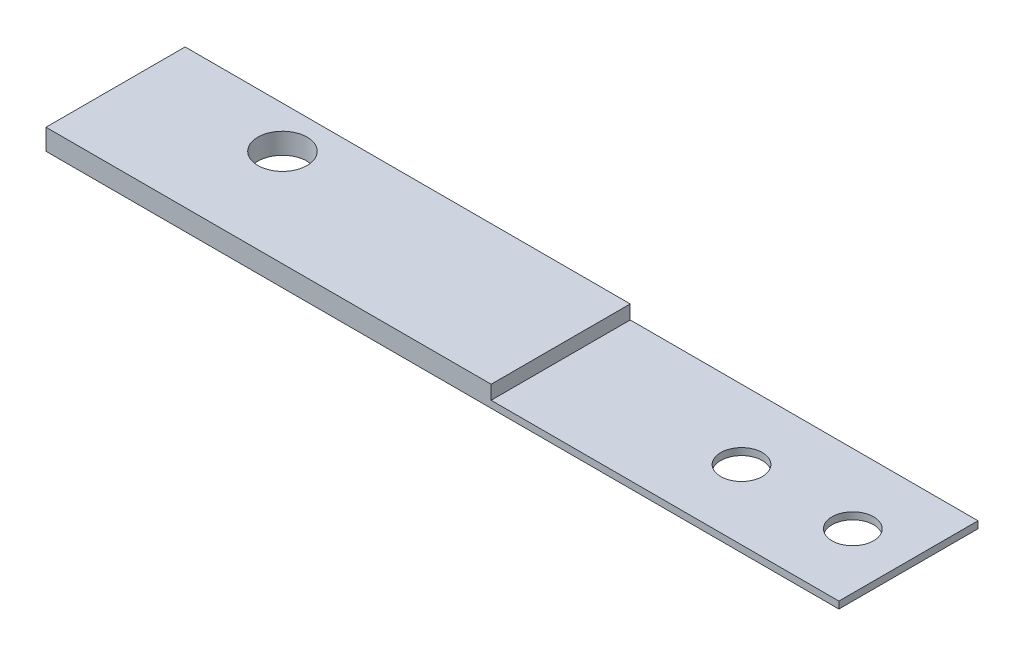
SolidWorks part; units mm, degrees
ref_plane "Front Plane" through (0, 0, 0) normal (0, 0, 1) x (1, 0, 0)
ref_plane "Top Plane" through (0, 0, 0) normal (0, 1, 0) x (1, 0, 0)
ref_plane "Right Plane" through (0, 0, 0) normal (1, 0, 0) x (0, 0, -1)
sketch "Sketch1" plane through (0, 0, 0) normal (0, 1, 0) x (1, 0, 0)
  line L1 (0, 0) -> (72.39, 0)
  line L2 (0, 0) -> (0, -12.7)
  line L3 (0, -12.7) -> (72.39, -12.7)
  line L4 (72.39, 0) -> (72.39, -12.7)
  dimension "D1" = 72.39
  dimension "D2" = 12.7
extrude "Boss-Extrude1" add sketch "Sketch1" along normal blind 0.635 contours L1 L4 L3 L2
sketch "Sketch2" plane through (0, 0.635, 0) normal (0, 1, 0) x (1, 0, 0)
  line L0 (0, -12.7) -> (72.39, -12.7) construction
  line L1 (0, 0) -> (40.64, 0)
  line L2 (0, 0) -> (0, -12.7)
  line L3 (0, -12.7) -> (40.64, -12.7)
  line L4 (40.64, 0) -> (40.64, -12.7)
  line L5 (72.39, 0) -> (72.39, -12.7) construction
  dimension "D1" = 31.75
extrude "Boss-Extrude2" add sketch "Sketch2" along normal blind 1.27
sketch "Sketch3" plane through (0, 0, 0) normal (0, -1, 0) x (1, 0, 0)
  line L0 (72.39, 0) -> (72.39, 12.7) construction
  line L1 (0, 0) -> (0, 12.7) construction
  line L2 (0, 0) -> (72.39, 0) construction
  line L3 (0, 12.7) -> (72.39, 12.7) construction
  point P0 (67.31, 6.35)
  point P1 (57.15, 6.35)
  point P2 (12.7, 3.81)
  dimension "D1" = 5.08
  dimension "D2" = 10.16
  dimension "D3" = 12.7
  dimension "D4" = 3.81
  dimension "D5" = 6.35
  dimension "D6" = 6.35
hole_wizard "#6 Clearance Hole1" positions "Sketch4" profile "Sketch5" hole size "#6" standard "ANSI Inch" end condition through all
sketch "Sketch4" plane through (0, 0, 0) normal (0, -1, 0) x (-1, 0, 0)
  point P0 (-67.31, -6.35)
  point P3 (-57.15, -6.35)
sketch "Sketch5" plane through (67.31, 0, 6.35) normal (1, 0, 0) x (0, 0, -1)
  line L0 (0, 0) -> (0, 1.905)
  line L1 (0, 1.905) -> (1.8986, 1.905)
  line L2 (1.8986, 1.905) -> (1.8986, 0)
  line L5 (1.8986, 0) -> (0, 0)
  line L11 (0, -6.35) -> (0, 107.95) construction
  dimension "Thru Hole Dia." = 3.7973
  dimension "Thru Hole Depth" = 1.905
hole_wizard "#8 Clearance Hole1" positions "Sketch6" profile "Sketch7" hole size "#8" standard "ANSI Inch" end condition through all
sketch "Sketch6" plane through (0, 0, 0) normal (0, -1, 0) x (-1, 0, 0)
  point P0 (-12.7, -3.81)
sketch "Sketch7" plane through (12.7, 0, 3.81) normal (1, 0, 0) x (0, 0, -1)
  line L0 (0, 0) -> (0, 1.905)
  line L1 (0, 1.905) -> (2.2479, 1.905)
  line L2 (2.2479, 1.905) -> (2.2479, 0)
  line L5 (2.2479, 0) -> (0, 0)
  line L11 (0, -6.35) -> (0, 107.95) construction
  dimension "Thru Hole Dia." = 4.4958
  dimension "Thru Hole Depth" = 1.905
sketch "Sketch9" plane through (0, 0, 0) normal (-1, 0, 0) x (0, 0, 1)
  line L0 (0, 0) -> (0.2933, 0.508)
  line L1 (0.2933, 0.508) -> (0.5866, 0)
  line L2 (0, 0) -> (12.7, 0) construction
  line L3 (0.5866, 0) -> (0.8799, 0.508)
  line L4 (0.8799, 0.508) -> (1.1732, 0)
  line L5 (1.27, 0) -> (1.5633, 0.508)
  line L6 (1.5633, 0.508) -> (1.8566, 0)
  line L7 (1.8566, 0) -> (2.1499, 0.508)
  line L8 (2.1499, 0.508) -> (2.4432, 0)
  line L9 (2.54, 0) -> (2.8333, 0.508)
  line L10 (2.8333, 0.508) -> (3.1266, 0)
  line L11 (3.1266, 0) -> (3.4199, 0.508)
  line L12 (3.4199, 0.508) -> (3.7132, 0)
  line L13 (3.81, 0) -> (4.1033, 0.508)
  line L14 (4.1033, 0.508) -> (4.3966, 0)
  line L15 (4.3966, 0) -> (4.6899, 0.508)
  line L16 (4.6899, 0.508) -> (4.9832, 0)
  line L17 (5.08, 0) -> (5.3733, 0.508)
  line L18 (5.3733, 0.508) -> (5.6666, 0)
  line L19 (5.6666, 0) -> (5.9599, 0.508)
  line L20 (5.9599, 0.508) -> (6.2532, 0)
  line L21 (6.35, 0) -> (6.6433, 0.508)
  line L22 (6.6433, 0.508) -> (6.9366, 0)
  line L23 (6.9366, 0) -> (7.2299, 0.508)
  line L24 (7.2299, 0.508) -> (7.5232, 0)
  line L25 (7.62, 0) -> (7.9133, 0.508)
  line L26 (7.9133, 0.508) -> (8.2066, 0)
  line L27 (8.2066, 0) -> (8.4999, 0.508)
  line L28 (8.4999, 0.508) -> (8.7932, 0)
  line L29 (8.89, 0) -> (9.1833, 0.508)
  line L30 (9.1833, 0.508) -> (9.4766, 0)
  line L31 (9.4766, 0) -> (9.7699, 0.508)
  line L32 (9.7699, 0.508) -> (10.0632, 0)
  line L33 (10.16, 0) -> (10.4533, 0.508)
  line L34 (10.4533, 0.508) -> (10.7466, 0)
  line L35 (10.7466, 0) -> (11.0399, 0.508)
  line L36 (11.0399, 0.508) -> (11.3332, 0)
  line L37 (11.43, 0) -> (11.7233, 0.508)
  line L38 (11.7233, 0.508) -> (12.0166, 0)
  line L39 (12.0166, 0) -> (12.3099, 0.508)
  line L40 (12.3099, 0.508) -> (12.6032, 0)
  line L41 (0, 0) -> (12.6032, 0)
  line M5 (0, 0) -> (12.7, 0)
  dimension "D1" = 60
  dimension "D2" = 60
  dimension "D3" = 0.508
  dimension "D4" = 60
  dimension "D5" = 0.508
  dimension "D6" = 60
  dimension "D7" = 10
extrude "Cut-Extrude6" cut sketch "Sketch9" against normal blind 10.16 and the other way through all contours L6 L5 M5 | L8 L7 M5 | L4 L3 M5 | L1 L0 M5 | L10 L9 M5 | L12 L11 M5 | L14 L13 M5 | L16 L15 M5 | L18 L17 M5 | L20 L19 M5 | L22 L21 M5 | L24 L23 M5 | L26 L25 M5 | L28 L27 M5 | L30 L29 M5 | L32 L31 M5 | L34 L33 M5 | L36 L35 M5 | L38 L37 M5 | L40 L39 M5
